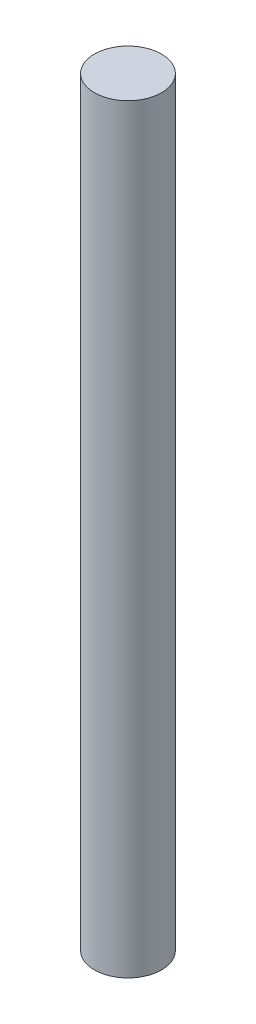
SolidWorks part; units mm, degrees
ref_plane "Top Plane" through (0, 0, 0) normal (0, 0, 1) x (1, 0, 0)
ref_plane "Front Plane" through (0, 0, 0) normal (0, 1, 0) x (1, 0, 0)
ref_plane "Right Plane" through (0, 0, 0) normal (1, 0, 0) x (0, 0, -1)
sketch "Profile Sketch" plane through (0, 0, 0) normal (0, 1, 0) x (1, 0, 0)
  circle A0 centre (0, 0) radius 4
  dimension "D1" = 8
extrude "Boss-Extrude1" add sketch "Profile Sketch" along normal blind 90.6018
